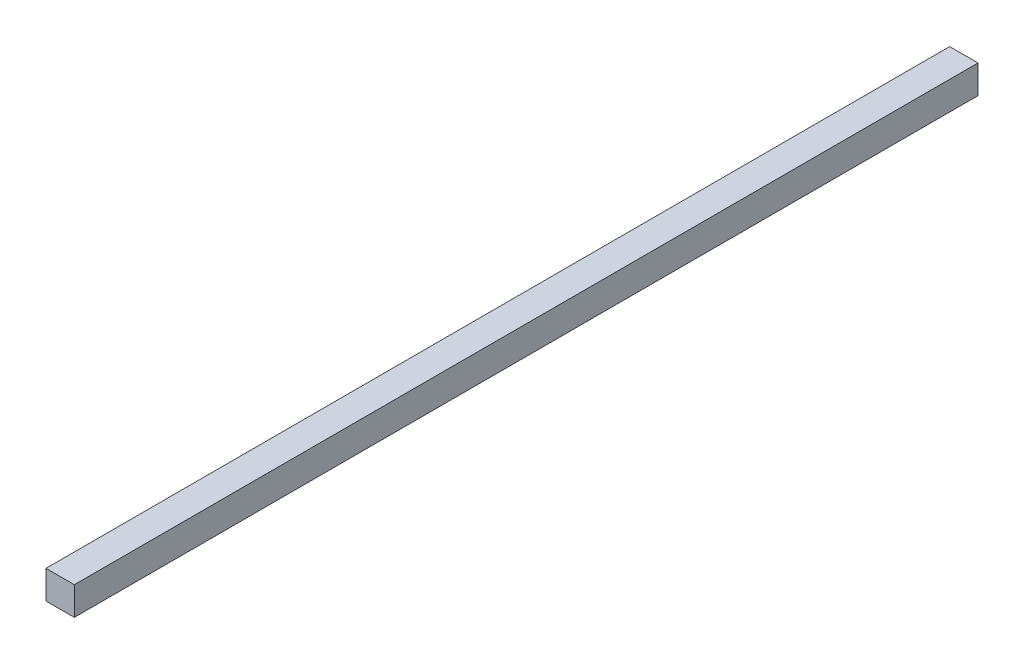
SolidWorks part; units mm, degrees
ref_plane "Face" through (0, 0, 0) normal (0, 0, 1) x (1, 0, 0)
ref_plane "Dessus" through (0, 0, 0) normal (0, 1, 0) x (1, 0, 0)
ref_plane "Droite" through (0, 0, 0) normal (1, 0, 0) x (0, 0, -1)
sketch "Esquisse1" plane through (0, 0, 0) normal (0, 0, 1) x (1, 0, 0)
  line L1 (0, 0) -> (18, 0)
  line L2 (0, 0) -> (0, 18)
  line L3 (0, 18) -> (18, 18)
  line L4 (18, 0) -> (18, 18)
  dimension "D1" = 18
  dimension "D2" = 18
extrude "Extrusion1" add sketch "Esquisse1" against normal blind 574
